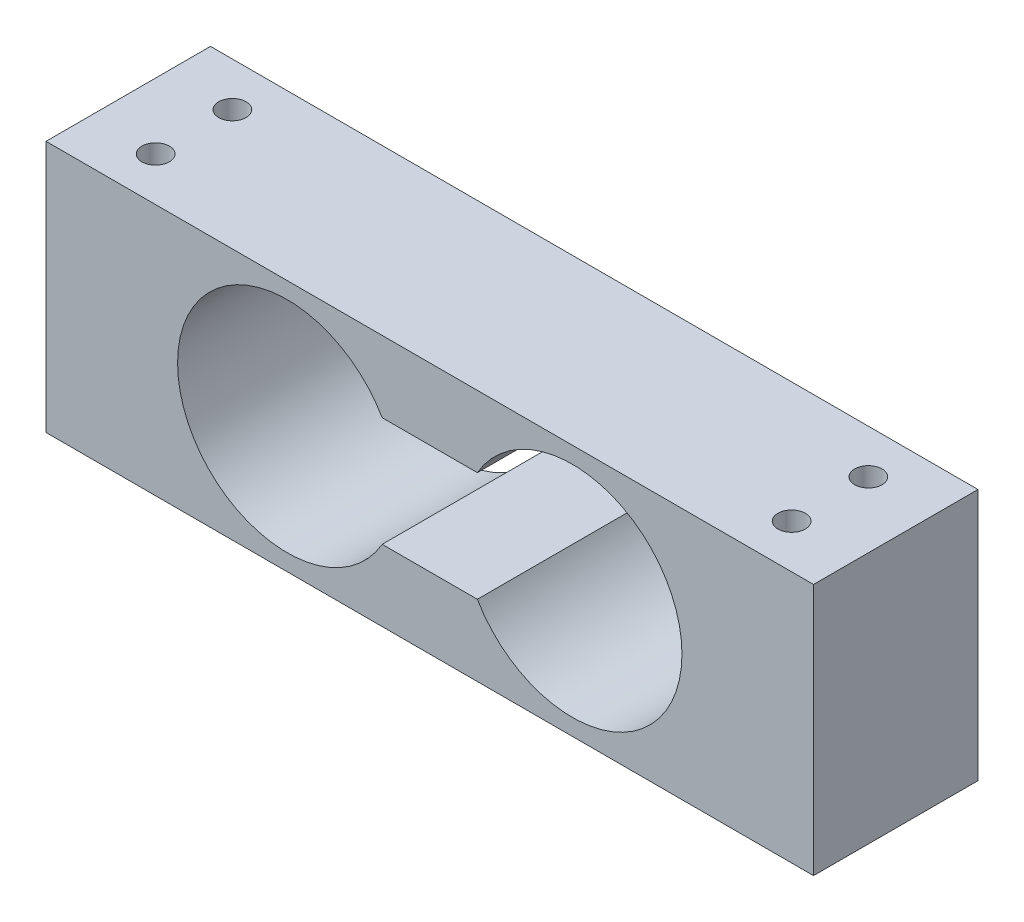
SolidWorks part; units mm, degrees
ref_plane "Plan de face" through (0, 0, 0) normal (0, 0, 1) x (1, 0, 0)
ref_plane "Plan de dessus" through (0, 0, 0) normal (0, 1, 0) x (1, 0, 0)
ref_plane "Plan de droite" through (0, 0, 0) normal (1, 0, 0) x (0, 0, -1)
sketch "Esquisse1" plane through (0, 0, 0) normal (0, 0, 1) x (1, 0, 0)
  line L0 (-70, 11.5) -> (-48, 11.5) construction
  line L1 (0, 0) -> (-70, 0)
  line L2 (0, 0) -> (0, 23)
  line L3 (0, 23) -> (-70, 23)
  line L4 (-70, 0) -> (-70, 23)
  line L5 (-48, 11.5) -> (-22, 11.5) construction
  line L6 (-22, 11.5) -> (0, 11.5) construction
  line L7 (-39.3397, 16.5) -> (-30.6603, 16.5)
  line L9 (-39.3397, 6.5) -> (-30.6603, 6.5)
  arc A0 (-39.3397, 16.5) -> (-39.3397, 6.5) centre (-48, 11.5) ccw
  arc A1 (-30.6603, 6.5) -> (-30.6603, 16.5) centre (-22, 11.5) ccw
  dimension "D4" = 20
  dimension "D1" = 70
  dimension "D2" = 23
  dimension "D3" = 26
  dimension "D5" = 5
  dimension "D6" = 5
extrude "Extrusion1" add sketch "Esquisse1" along normal mid plane 15
hole_wizard "Trou taraudé M3x0.51" positions "Esquisse3D1" profile "Esquisse2" tap size "M3x0.5" standard "ISO" end condition through all
sketch3d "Esquisse3D1"
  line L0 (-64, 23, -3.5) -> (-64, 23, 3.5) construction
  line L1 (-6, 23, -3.5) -> (-6, 23, 3.5) construction
  line L5 (-64, 23, 3.5) -> (-6, 23, 3.5) construction
  line L6 (-6, 23, -3.5) -> (-64, 23, -3.5) construction
  line L8 (0, 23, -7.5) -> (-70, 23, -7.5) construction
  line L10 (-70, 23, 7.5) -> (-70, 23, -7.5) construction
  line L11 (0, 23, 7.5) -> (0, 23, -7.5) construction
  line L12 (-70, 23, 0) -> (-64, 23, 0) construction
  point P0 (-64, 23, -3.5)
  point P2 (-64, 23, 3.5)
  point P4 (-6, 23, -3.5)
  point P6 (-6, 23, 3.5)
  dimension "D1" = 7
  dimension "D2" = 6
  dimension "D3" = 6
cosmetic thread "Filetage de perçage1" parameters "D2"=3
cosmetic thread "Filetage de perçage2" parameters "D2"=3
cosmetic thread "Filetage de perçage3" parameters "D2"=3
cosmetic thread "Filetage de perçage4" parameters "D2"=3
sketch "Esquisse2" plane through (-64, 23, -3.5) normal (1, 0, 0) x (0, 0, 1)
  line L0 (0, 0) -> (0, 23)
  line L1 (0, 23) -> (1.25, 23)
  line L2 (1.25, 23) -> (1.25, 0)
  line L5 (1.25, 0) -> (0, 0)
  line L11 (0, -6.35) -> (0, 107.95) construction
  dimension "Diamètre du trou pour taraudage jusqu'au prochain" = 2.5
  dimension "Profondeur du trou pour taraudage jusqu'au prochain" = 23
